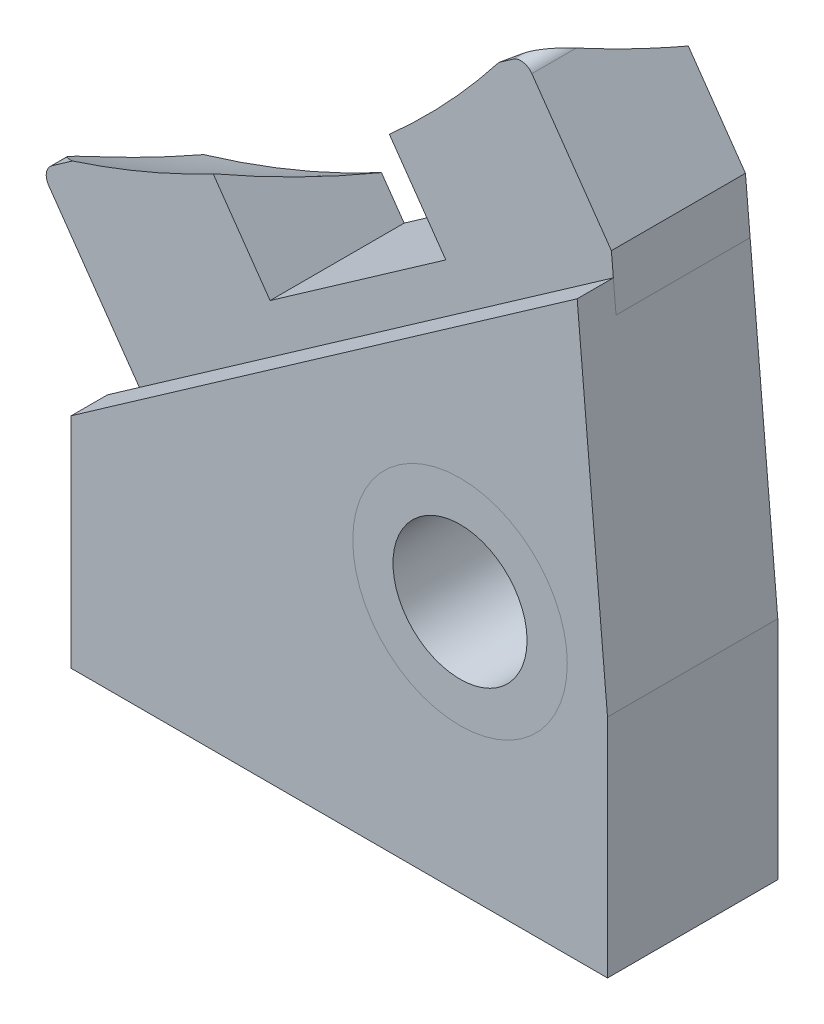
SolidWorks part; units mm, degrees
ref_plane "Ebene vorne" through (0, 0, 0) normal (0, 0, 1) x (1, 0, 0)
ref_plane "Ebene oben" through (0, 0, 0) normal (0, 1, 0) x (1, 0, 0)
ref_plane "Ebene rechts" through (0, 0, 0) normal (1, 0, 0) x (0, 0, -1)
sketch "Skizze1" plane through (0, 0, 0) normal (0, 0, 1) x (1, 0, 0)
  line L0 (20, 8.4286) -> (18.8678, 21.37)
  line L1 (0, 30.625) -> (0, -33.9904) construction
  line L2 (18.8678, 21.37) -> (0, 8.1586)
  line L3 (0, 8.1586) -> (0, 0)
  line L4 (18.8678, 21.37) -> (5.1999, 21.37) construction
  line L6 (20, 8.4286) -> (20, 0)
  line L7 (20, 0) -> (0, 0)
  circle A0 centre (14.5, 9.4) radius 4
  point P9 (0, 0)
  dimension "D6" = 8
  dimension "D1" = 20
  dimension "D2" = 21.37
  dimension "D3" = 5
  dimension "D4" = 7.3
  dimension "D5" = 35
  dimension "D7" = 5.5
  dimension "D8" = 9.4
extrude "Aufsatz-Linear austragen1" add sketch "Skizze1" along normal blind 6.35
sketch "Skizze3" plane through (-3.8333, 5.4745, 0) normal (-0.5736, 0.8192, 0) x (0.8192, 0.5736, 0)
  line L1 (27.7129, -6.35) -> (27.7129, 0) construction
  line L2 (0, 0) -> (27.7129, 0)
  line L3 (0, 0) -> (0, -5)
  line L4 (0, -5) -> (27.7129, -5)
  line L5 (27.7129, 0) -> (27.7129, -5)
  dimension "D1" = 5
extrude "Schnitt-Linear austragen1" cut sketch "Skizze3" against normal blind 1
sketch "Skizze4" plane through (0, 0, 5) normal (0, 0, -1) x (-1, 0, 0)
  line L0 (-18.7941, 22.2121) -> (-18.9684, 20.2197)
  line L1 (-18.7941, 22.2121) -> (-15.8299, 26.4454)
  line L2 (-15.1335, 26.5682) -> (-9.809, 22.84)
  line L3 (2.1915, 13.8267) -> (-1.7662, 8.1746)
  line L4 (-1.7662, 8.1746) -> (-18.9684, 20.2197)
  line L5 (-18.8678, 21.37) -> (0, 8.1586) construction
  line L6 (-6.5324, 20.5457) -> (-10.7769, 14.4839) construction
  line L7 (-3.2558, 18.2513) -> (-6.0663, 14.2375)
  line L8 (-6.0663, 14.2375) -> (-12.6196, 18.8261)
  line L9 (-9.809, 22.84) -> (-12.6196, 18.8261)
  line L10 (-3.2558, 18.2513) -> (2.0687, 14.5231)
  line L11 (-3.2558, 18.2513) -> (-6.5324, 20.5457) construction
  line L12 (-6.5324, 20.5457) -> (-9.809, 22.84) construction
  line L13 (-18.9684, 20.2197) -> (-18.8678, 21.37) construction
  line L14 (-18.9684, 20.2197) -> (0, 6.9379) construction
  arc A0 (-15.8299, 26.4454) -> (-15.1335, 26.5682) centre (-15.4203, 26.1586) cw
  arc A1 (2.0687, 14.5231) -> (2.1915, 13.8267) centre (1.7819, 14.1135) cw
  point P16 (-9.3429, 16.5318)
  point P22 (2.4782, 14.2363)
  point P24 (8.1288, 44.9335)
  dimension "D5" = 0.5
  dimension "D1" = 22
  dimension "D2" = 7.4
  dimension "D3" = 8
  dimension "D4" = 2.5
  dimension "D7" = 1
extrude "Aufsatz-Linear austragen2" add sketch "Skizze4" along normal blind 5 separate body
ref_plane "Ebene1" through (0, 0, -12.575) normal (0, 0, 1) x (1, 0, 0)
sketch "Skizze5" plane through (0, 0, -12.575) normal (0, 0, 1) x (1, 0, 0)
  line L0 (20, 0) -> (20, 8.4286) construction
  line L1 (0, 0) -> (20, 0) construction
  line L2 (-48.8465, 46.47) -> (25.9465, 46.47)
  arc A0 (-48.8465, 46.47) -> (25.9465, 46.47) centre (-11.45, 46.47) ccw
  dimension "D1" = 31.45
  dimension "D3" = 74.793
  dimension "D2" = 46.47
revolve "Schnitt-Rotation1" cut sketch "Skizze5" angle 360 about L2
sketch "Skizze6" plane through (0, 0, 6.35) normal (0, 0, 1) x (1, 0, 0)
  circle A0 centre (14.5, 9.4) radius 4
  circle A1 centre (14.5, 9.4) radius 2.5
  dimension "D1" = 5
  dimension "D2" = 8
extrude "Aufsatz-Linear austragen3" add sketch "Skizze6" against normal blind 6.35 separate body
